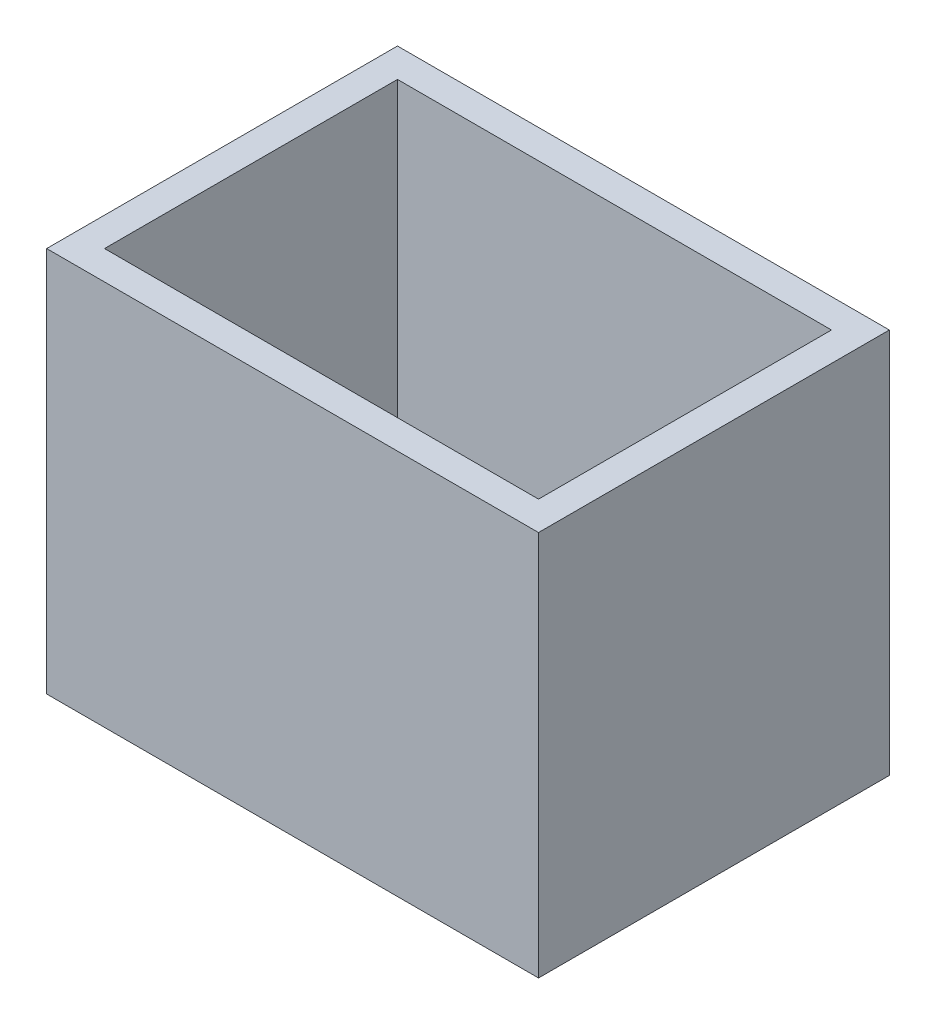
SolidWorks part; units mm, degrees
ref_plane "前视基准面" through (0, 0, 0) normal (0, 0, 1) x (1, 0, 0)
ref_plane "上视基准面" through (0, 0, 0) normal (0, 1, 0) x (1, 0, 0)
ref_plane "右视基准面" through (0, 0, 0) normal (1, 0, 0) x (0, 0, -1)
sketch "草图1" plane through (0, 0, 0) normal (0, 1, 0) x (1, 0, 0)
  line L0 (0, 0) -> (0, -2430) construction
  line L1 (0, -2430) -> (3600, -2430) construction
  line L2 (3600, 0) -> (3600, -2430) construction
  line L3 (0, 0) -> (3600, 0) construction
  line L4 (0, 0) -> (0, -2430)
  line L5 (0, -2430) -> (3600, -2430)
  line L6 (3600, 0) -> (3600, -2430)
  line L7 (0, 0) -> (3600, 0)
extrude "拉伸-薄壁1" add sketch "草图1" along normal blind 1200 and the other way blind 2000 thin
